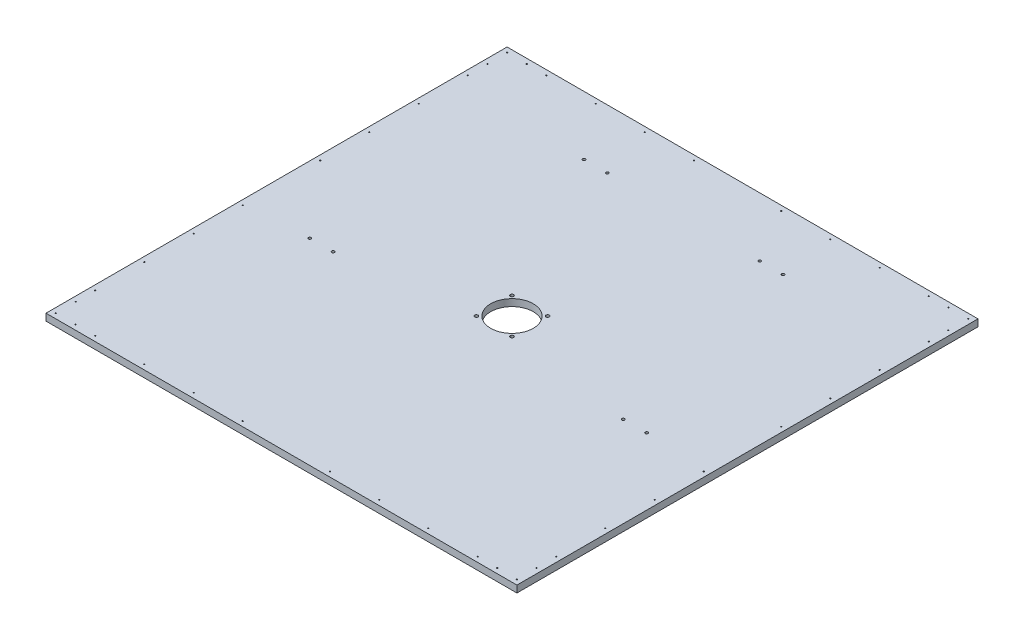
SolidWorks part; units mm, degrees
ref_plane "Front Plane" through (0, 0, 0) normal (0, 0, 1) x (1, 0, 0)
ref_plane "Top Plane" through (0, 0, 0) normal (0, 1, 0) x (1, 0, 0)
ref_plane "Right Plane" through (0, 0, 0) normal (1, 0, 0) x (0, 0, -1)
sketch "Sketch1" plane through (0, 0, 0) normal (0, 1, 0) x (1, 0, 0)
  line L1 (0, 0) -> (1216.025, 0)
  line L2 (0, 0) -> (0, -1190.625)
  line L3 (0, -1190.625) -> (1216.025, -1190.625)
  line L4 (1216.025, 0) -> (1216.025, -1190.625)
  dimension "D1" = 1216.025
  dimension "D2" = 1190.625
extrude "Boss-Extrude1" add sketch "Sketch1" along normal blind 17.8562
sketch "Sketch2" plane through (0, 17.8562, 0) normal (0, 1, 0) x (1, 0, 0)
  line L0 (541.1122, -552.5135) -> (545.5316, -564.4197) construction
  line L1 (525.4625, -652.526) -> (690.5625, -652.526) construction
  line L2 (525.4625, -652.526) -> (525.4625, -538.226) construction
  line L3 (525.4625, -538.226) -> (690.5625, -538.226) construction
  line L4 (690.5625, -652.526) -> (690.5625, -538.226) construction
  line L5 (547.8094, -550.0276) -> (552.2288, -561.9338) construction
  line L6 (534.4149, -554.9994) -> (538.8343, -566.9057) construction
  line L7 (525.4625, -595.376) -> (690.5625, -595.376) construction
  line L8 (608.0125, -538.226) -> (608.0125, -652.526) construction
  line L9 (670.4934, -564.4197) -> (674.9128, -552.5135) construction
  line L10 (663.7962, -561.9338) -> (668.2156, -550.0276) construction
  line L11 (677.1907, -566.9057) -> (681.6101, -554.9994) construction
  line L12 (670.4934, -626.3323) -> (674.9128, -638.2385) construction
  line L13 (677.1907, -623.8463) -> (681.6101, -635.7526) construction
  line L14 (663.7962, -628.8182) -> (668.2156, -640.7244) construction
  line L15 (541.1122, -638.2385) -> (545.5316, -626.3323) construction
  line L16 (534.4149, -635.7526) -> (538.8343, -623.8463) construction
  line L17 (547.8094, -640.7244) -> (552.2288, -628.8182) construction
  line L18 (543.3219, -538.226) -> (543.3219, -558.4666) construction
  line L19 (543.3219, -558.4666) -> (543.3219, -632.2854) construction
  line L20 (543.3219, -632.2854) -> (543.3219, -652.526) construction
  line L21 (525.4625, -558.4666) -> (543.3219, -558.4666) construction
  line L22 (543.3219, -558.4666) -> (672.7031, -558.4666) construction
  line L23 (672.7031, -558.4666) -> (690.5625, -558.4666) construction
  line L24 (589.7, -584.8033) -> (608.0125, -595.376) construction
  line L25 (608.0125, -595.376) -> (608.0125, -616.5215) construction
  line L26 (608.0125, -595.376) -> (626.325, -584.8032) construction
  line L27 (1216.025, 0) -> (0, 0) construction
  arc A0 (547.8094, -550.0276) -> (534.4149, -554.9994) centre (541.1122, -552.5135) ccw construction
  arc A1 (538.8343, -566.9057) -> (552.2288, -561.9338) centre (545.5316, -564.4197) ccw construction
  arc A2 (663.7962, -561.9338) -> (677.1907, -566.9057) centre (670.4934, -564.4197) ccw construction
  arc A3 (681.6101, -554.9994) -> (668.2156, -550.0276) centre (674.9128, -552.5135) ccw construction
  arc A4 (677.1907, -623.8463) -> (663.7962, -628.8182) centre (670.4934, -626.3323) ccw construction
  arc A5 (668.2156, -640.7244) -> (681.6101, -635.7526) centre (674.9128, -638.2385) ccw construction
  arc A6 (534.4149, -635.7526) -> (547.8094, -640.7244) centre (541.1122, -638.2385) ccw construction
  arc A7 (552.2288, -628.8182) -> (538.8343, -623.8463) centre (545.5316, -626.3323) ccw construction
  circle A8 centre (608.0125, -595.376) radius 21.1455 construction
  circle A9 centre (589.7, -584.8033) radius 2.1971
  circle A10 centre (608.0125, -616.5215) radius 2.1971
  circle A11 centre (626.325, -584.8032) radius 2.1971
  circle A12 centre (541.1122, -552.5135) radius 7.1437
  circle A13 centre (674.9128, -552.5135) radius 7.1437
  circle A14 centre (674.9128, -638.2385) radius 7.1437
  circle A15 centre (541.1122, -638.2385) radius 7.1437
  point P6 (543.3219, -558.4666)
  point P15 (672.7031, -558.4666)
  point P22 (672.7031, -632.2854)
  point P29 (543.3219, -632.2854)
  point P61 (608.0125, 0)
  dimension "D8" = 42.291
  dimension "D9" = 4.3942
  dimension "D1" = 114.3
  dimension "D2" = 165.1
  dimension "D3" = 14.2875
  dimension "D4" = 129.3812
  dimension "D5" = 73.8188
  dimension "D6" = 12.7
  dimension "D7" = 85.725
  dimension "D10" = 120
  dimension "D11" = 120
  dimension "D12" = 595.376
sketch "Sketch3" plane through (0, 17.8562, 0) normal (0, 1, 0) x (1, 0, 0)
  circle A0 centre (608.0125, -595.376) radius 55
  dimension "D1" = 110
extrude "Cut-Extrude1" cut sketch "Sketch3" against normal through all both and the other way through all
sketch "Sketch4" plane through (0, 17.8562, 0) normal (0, 1, 0) x (1, 0, 0)
  line L1 (562.0506, -549.4141) -> (653.9744, -549.4141) construction
  line L2 (562.0506, -549.4141) -> (562.0506, -641.3379) construction
  line L3 (562.0506, -641.3379) -> (653.9744, -641.3379) construction
  line L4 (653.9744, -549.4141) -> (653.9744, -641.3379) construction
  circle A0 centre (608.0125, -595.376) radius 65 construction
  circle A1 centre (562.0506, -549.4141) radius 4.25
  circle A2 centre (653.9744, -549.4141) radius 4.25
  circle A3 centre (653.9744, -641.3379) radius 4.25
  circle A4 centre (562.0506, -641.3379) radius 4.25
  dimension "D1" = 130
  dimension "D2" = 8.5
extrude "Cut-Extrude2" cut sketch "Sketch4" against normal through all both
sketch "Sketch5" plane through (0, 17.8562, 0) normal (0, 1, 0) x (1, 0, 0)
  line L0 (0, 0) -> (0, -1190.625) construction
  line L1 (1216.025, 0) -> (0, 0) construction
  line L2 (12.7, -12.7) -> (12.7, -63.5) construction
  line L3 (12.7, -63.5) -> (12.7, -114.3) construction
  line L4 (12.7, -12.7) -> (63.5, -12.7) construction
  line L5 (63.5, -12.7) -> (114.3, -12.7) construction
  line L6 (0, -595.3125) -> (1216.025, -595.3125) construction
  line L7 (1216.025, -1190.625) -> (1216.025, 0) construction
  line L8 (608.0125, 0) -> (608.0125, -1190.625) construction
  line L9 (0, -1190.625) -> (1216.025, -1190.625) construction
  line L10 (1152.525, -12.7) -> (1101.725, -12.7) construction
  line L11 (1203.325, -12.7) -> (1152.525, -12.7) construction
  line L12 (1203.325, -63.5) -> (1203.325, -114.3) construction
  line L13 (1203.325, -12.7) -> (1203.325, -63.5) construction
  line L14 (1203.325, -1177.925) -> (1203.325, -1127.125) construction
  line L15 (1203.325, -1127.125) -> (1203.325, -1076.325) construction
  line L16 (1203.325, -1177.925) -> (1152.525, -1177.925) construction
  line L17 (1152.525, -1177.925) -> (1101.725, -1177.925) construction
  line L18 (63.5, -1177.925) -> (114.3, -1177.925) construction
  line L19 (12.7, -1177.925) -> (63.5, -1177.925) construction
  line L20 (12.7, -1127.125) -> (12.7, -1076.325) construction
  line L21 (12.7, -1177.925) -> (12.7, -1127.125) construction
  circle A0 centre (12.7, -12.7) radius 1.3891
  circle A1 centre (12.7, -63.5) radius 1.3891
  circle A2 centre (63.5, -12.7) radius 1.3891
  circle A3 centre (12.7, -114.3) radius 1.3891
  circle A4 centre (114.3, -12.7) radius 1.3891
  circle A5 centre (12.7, -241.3) radius 1.3891
  circle A6 centre (12.7, -368.3) radius 1.3891
  circle A7 centre (12.7, -495.3) radius 1.3891
  circle A11 centre (241.3, -12.7) radius 1.3891
  circle A12 centre (368.3, -12.7) radius 1.3891
  circle A13 centre (495.3, -12.7) radius 1.3891
  circle A14 centre (720.725, -12.7) radius 1.3891
  circle A15 centre (847.725, -12.7) radius 1.3891
  circle A16 centre (974.725, -12.7) radius 1.3891
  circle A17 centre (1203.325, -495.3) radius 1.3891
  circle A18 centre (1203.325, -368.3) radius 1.3891
  circle A19 centre (1203.325, -241.3) radius 1.3891
  circle A20 centre (1101.725, -12.7) radius 1.3891
  circle A21 centre (1203.325, -114.3) radius 1.3891
  circle A22 centre (1152.525, -12.7) radius 1.3891
  circle A23 centre (1203.325, -63.5) radius 1.3891
  circle A24 centre (1203.325, -12.7) radius 1.3891
  circle A25 centre (1203.325, -1177.925) radius 1.3891
  circle A26 centre (1203.325, -1127.125) radius 1.3891
  circle A27 centre (1152.525, -1177.925) radius 1.3891
  circle A28 centre (1203.325, -1076.325) radius 1.3891
  circle A29 centre (1101.725, -1177.925) radius 1.3891
  circle A30 centre (1203.325, -949.325) radius 1.3891
  circle A31 centre (1203.325, -822.325) radius 1.3891
  circle A32 centre (1203.325, -695.325) radius 1.3891
  circle A33 centre (974.725, -1177.925) radius 1.3891
  circle A34 centre (847.725, -1177.925) radius 1.3891
  circle A35 centre (720.725, -1177.925) radius 1.3891
  circle A36 centre (495.3, -1177.925) radius 1.3891
  circle A37 centre (368.3, -1177.925) radius 1.3891
  circle A38 centre (241.3, -1177.925) radius 1.3891
  circle A39 centre (12.7, -695.325) radius 1.3891
  circle A40 centre (12.7, -822.325) radius 1.3891
  circle A41 centre (12.7, -949.325) radius 1.3891
  circle A42 centre (114.3, -1177.925) radius 1.3891
  circle A43 centre (12.7, -1076.325) radius 1.3891
  circle A44 centre (63.5, -1177.925) radius 1.3891
  circle A45 centre (12.7, -1127.125) radius 1.3891
  circle A46 centre (12.7, -1177.925) radius 1.3891
  dimension "D1" = 2.7781
  dimension "D2" = 12.7
  dimension "D3" = 12.7
  dimension "D4" = 12.7
  dimension "D5" = 127
  dimension "D6" = 50.8
  dimension "D7" = 12.7
  dimension "D8" = 127
  dimension "D9" = 127
  dimension "D10" = 127
  dimension "D11" = 127
  dimension "D12" = 127
extrude "Cut-Extrude3" cut sketch "Sketch5" against normal through all both and the other way through all
sketch "Sketch8 - experimenting with yaw" plane through (0, 17.8562, 0) normal (0, 1, 0) x (1, 0, 0)
  line L0 (0, -799.277) -> (0, 0) construction
  line L2 (322.2625, -893.7625) -> (893.7625, -893.7625) construction
  line L5 (0, 0) -> (0, -1190.625) construction
  line L6 (322.2625, -893.7625) -> (322.2625, 0) construction
  line L7 (0, -1190.625) -> (1216.025, -1190.625) construction
  line L8 (1216.025, 0) -> (0, 0) construction
  line L9 (893.7625, -893.7625) -> (893.7625, 0) construction
  line L10 (893.7625, 0) -> (322.2625, 0) construction
  line L11 (1216.025, -1190.625) -> (1216.025, 0) construction
  line L12 (0, -957.424) -> (0, -1190.625) construction
  line L13 (-23.973, -823.25) -> (835.8865, 36.6095) construction
  line L14 (-23.973, -823.25) -> (817.926, -1665.149) construction
  line L15 (817.926, -1665.149) -> (1677.7855, -805.2895) construction
  line L16 (835.8865, 36.6095) -> (1677.7855, -805.2895) construction
  line L17 (0, -1190.625) -> (233.201, -1190.625) construction
  line L18 (562.997, -1190.625) -> (1216.025, -1190.625) construction
  line L19 (1216.025, -1190.625) -> (1216.025, -537.597) construction
  line L20 (0, 0) -> (489.651, 0) construction
  circle A0 centre (608.0125, -595.376) radius 55 construction
  dimension "D3" = 110
  dimension "D1" = 296.8625
  dimension "D2" = 322.2625
  dimension "D4" = 322.2625
  dimension "D5" = 285.75
  dimension "D6" = 608.0125
  dimension "D7" = 45
  dimension "D8" = 653.028
  dimension "D9" = 653.028
  dimension "D10" = 233.201
  dimension "D11" = 233.201
  dimension "D12" = 489.651
  dimension "D13" = 799.277
sketch "Sketch9" plane through (0, 17.8562, 0) normal (0, 1, 0) x (1, 0, 0)
  line L0 (0, -1190.625) -> (0, -537.597) construction
  line L1 (0, 0) -> (0, -1190.625) construction
  line L2 (0, -537.597) -> (653.028, -1190.625) construction
  line L3 (0, -1190.625) -> (1216.025, -1190.625) construction
  line L4 (653.028, -1190.625) -> (0, -1190.625) construction
  line L5 (1216.025, -1190.625) -> (1216.025, -537.597) construction
  line L6 (1216.025, -1190.625) -> (1216.025, 0) construction
  line L7 (1216.025, -537.597) -> (562.997, -1190.625) construction
  line L8 (562.997, -1190.625) -> (1216.025, -1190.625) construction
  line L9 (0, -489.651) -> (489.651, 0) construction
  line L10 (1216.025, 0) -> (0, 0) construction
  line L11 (726.374, 0) -> (1216.025, -489.651) construction
  dimension "D1" = 653.028
  dimension "D2" = 489.651
  dimension "D3" = 489.651
  dimension "D4" = 489.651
  dimension "D5" = 489.651
sketch "Sketch10" plane through (0, 17.8562, 0) normal (0, 1, 0) x (1, 0, 0)
  line L0 (1216.025, 0) -> (0, 0) construction
  line L1 (0, 0) -> (0, -1190.625) construction
  line L2 (1216.025, -1190.625) -> (1216.025, 0) construction
  line L3 (653.028, -1190.625) -> (0, -1190.625) construction
  line L4 (173.0375, -682.625) -> (233.3625, -682.625) construction
  line L5 (350.8375, -152.4) -> (411.1625, -152.4) construction
  line L6 (804.8625, -152.4) -> (865.1875, -152.4) construction
  line L8 (982.6625, -682.625) -> (1042.9875, -682.625) construction
  circle A0 centre (381, -152.4) radius 12.7 construction
  circle A1 centre (203.2, -682.625) radius 12.7 construction
  circle A2 centre (1012.825, -682.625) radius 12.7 construction
  circle A3 centre (835.025, -152.4) radius 12.7 construction
  circle A4 centre (173.0375, -682.625) radius 3.5719
  circle A5 centre (233.3625, -682.625) radius 3.5719
  circle A6 centre (350.8375, -152.4) radius 3.5719
  circle A7 centre (411.1625, -152.4) radius 3.5719
  circle A8 centre (804.8625, -152.4) radius 3.5719
  circle A9 centre (865.1875, -152.4) radius 3.5719
  circle A12 centre (982.6625, -682.625) radius 3.5719
  circle A13 centre (1042.9875, -682.625) radius 3.5719
  point P10 (203.2, -682.625)
  point P13 (381, -152.4)
  point P29 (835.025, -152.4)
  point P39 (1012.825, -682.625)
  dimension "D1" = 25.4
  dimension "D8" = 7.1437
  dimension "D10" = 7.1437
  dimension "D12" = 7.1437
  dimension "D16" = 7.1437
  dimension "D2" = 152.4
  dimension "D3" = 381
  dimension "D4" = 381
  dimension "D5" = 203.2
  dimension "D6" = 203.2
  dimension "D7" = 508
  dimension "D9" = 60.325
  dimension "D11" = 60.325
  dimension "D13" = 60.325
  dimension "D17" = 60.325
extrude "Cut-Extrude4" cut sketch "Sketch10" against normal through all both and the other way through all
